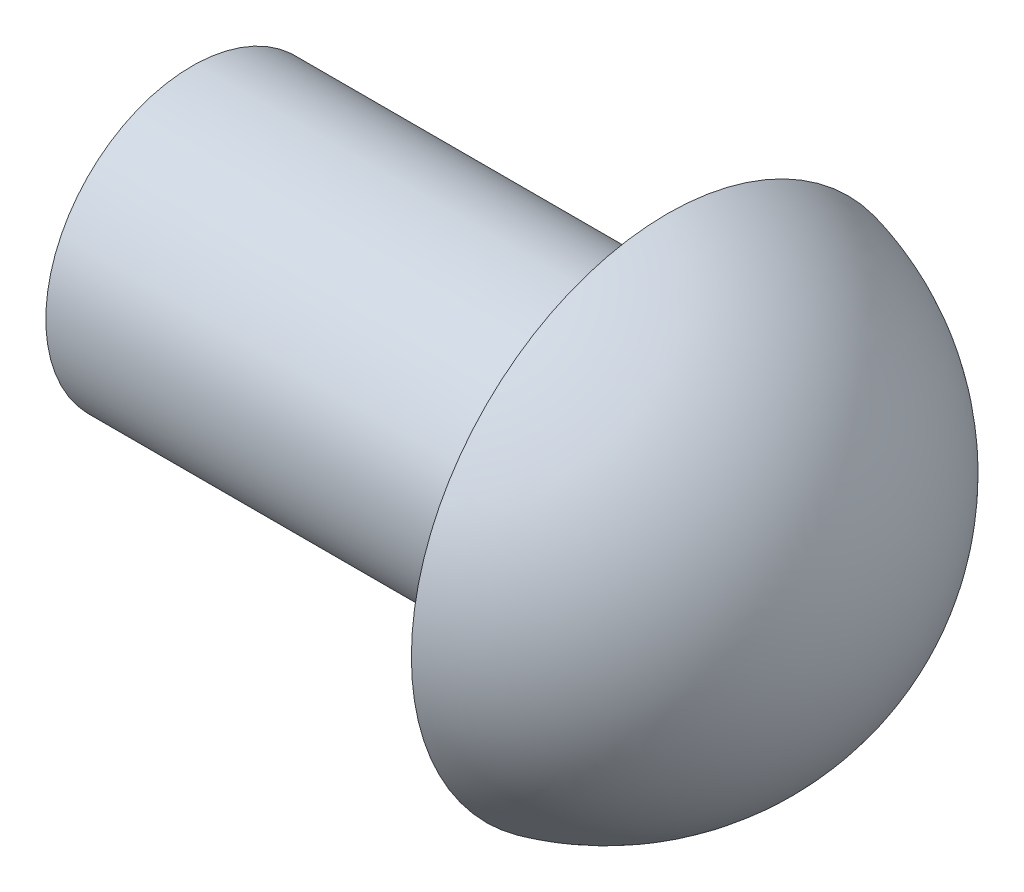
SolidWorks part; units mm, degrees
ref_plane "Front Plane" through (0, 0, 0) normal (0, 0, 1) x (1, 0, 0)
ref_plane "Top Plane" through (0, 0, 0) normal (0, 1, 0) x (1, 0, 0)
ref_plane "Right Plane" through (0, 0, 0) normal (1, 0, 0) x (0, 0, -1)
sketch "Sketch1" plane through (0, 0, 0) normal (1, 0, 0) x (0, 0, -1)
  circle A0 centre (0, 0) radius 2
extrude "Boss-Extrude1" add sketch "Sketch1" along normal blind 6.5
sketch "Sketch2" plane through (0, 0, 0) normal (0, 1, 0) x (1, 0, 0)
  line L0 (3.5719, 0) -> (9.2601, 0) construction
  line L1 (9.2601, 0) -> (6.5, 0)
  line L2 (6.5, -2) -> (6.5, 2) construction
  line L3 (6.5, 0) -> (6.5, 3.5)
  arc A0 (9.2601, 0) -> (6.5, 3.5) centre (5.6601, -0.0007) ccw
revolve "Revolve1" add sketch "Sketch2" angle 360 about L0
